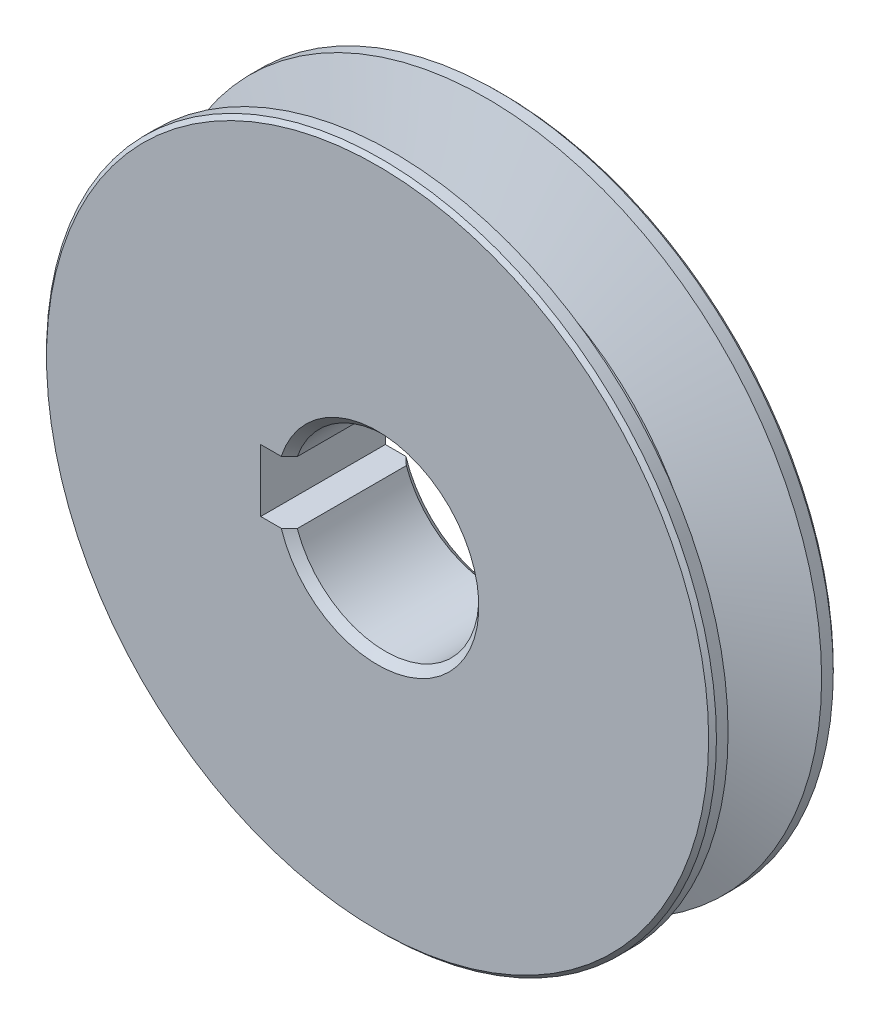
SolidWorks part; units mm, degrees
ref_plane "Front Plane" through (0, 0, 0) normal (0, 0, 1) x (1, 0, 0)
ref_plane "Top Plane" through (0, 0, 0) normal (0, 1, 0) x (1, 0, 0)
ref_plane "Right Plane" through (0, 0, 0) normal (1, 0, 0) x (0, 0, -1)
sketch "Sketch1" plane through (0, 0, 0) normal (0, 1, 0) x (1, 0, 0)
  line L0 (43, 8) -> (0, 8)
  line L1 (0, 8) -> (0, -8)
  line L2 (0, -8) -> (43, -8)
  line L3 (43, -8) -> (43, -6.0037)
  line L4 (43, -6.0037) -> (32, -2)
  line L5 (32, -2) -> (32, 2)
  line L6 (32, 2) -> (43, 6.0037)
  line L7 (43, 6.0037) -> (43, 8)
  line L8 (0, 8) -> (0, -8) construction
revolve "Revolve1" add sketch "Sketch1" angle 360 about L8
sketch "Sketch2" plane through (0, 0, 8) normal (0, 0, 1) x (1, 0, 0)
  line L0 (-15, -4) -> (-11.3137, -4)
  line L1 (-11.3137, 4) -> (-15, 4)
  line L2 (-15, 4) -> (-15, -4)
  arc A0 (-11.3137, -4) -> (-11.3137, 4) centre (0, 0) cw
extrude "Cut-Extrude1" cut sketch "Sketch2" against normal through all
sketch "Sketch3" plane through (0, 0, 0) normal (0, 1, 0) x (1, 0, 0)
  line L0 (12, 8) -> (0, 8)
  line L1 (0, 8) -> (0, -8)
  line L2 (0, -8) -> (12, -8)
  line L3 (12, -8) -> (12, 8)
  line L4 (0, 8) -> (0, -8) construction
revolve "Cut-Revolve1" cut sketch "Sketch3" angle 360 about L4
chamfer "Chamfer1" distance 1 angle 45 2 edges at (12, 0, 8) (12, 0, -8)
chamfer "Chamfer2" distance 0.5 angle 45 2 edges at (43, 0, 8) (43, 0, -8)
scale "Scale1" scale about centroid uniform scaling yes scale factor 0.3
